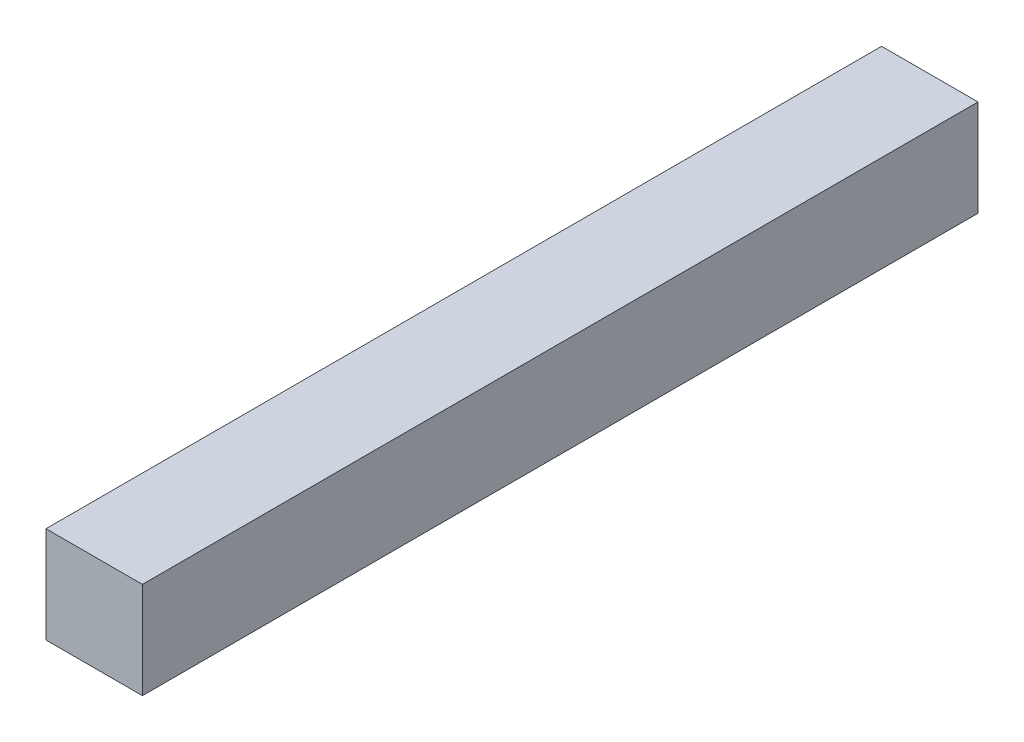
SolidWorks part; units mm, degrees
ref_plane "Front Plane" through (0, 0, 0) normal (0, 0, 1) x (1, 0, 0)
ref_plane "Top Plane" through (0, 0, 0) normal (0, 1, 0) x (1, 0, 0)
ref_plane "Right Plane" through (0, 0, 0) normal (1, 0, 0) x (0, 0, -1)
sketch "Sketch1" plane through (0, 0, 0) normal (0, 0, 1) x (1, 0, 0)
  line L1 (0.75, -0.75) -> (-0.75, -0.75)
  line L2 (0.75, -0.75) -> (0.75, 0.75)
  line L3 (0.75, 0.75) -> (-0.75, 0.75)
  line L4 (-0.75, -0.75) -> (-0.75, 0.75)
  line L5 (0.75, -0.75) -> (-0.75, 0.75) construction
  line L6 (0.75, 0.75) -> (-0.75, -0.75) construction
  point P0 (0, 0)
  dimension "D1" = 1.5
extrude "Boss-Extrude1" add sketch "Sketch1" along normal blind 13
